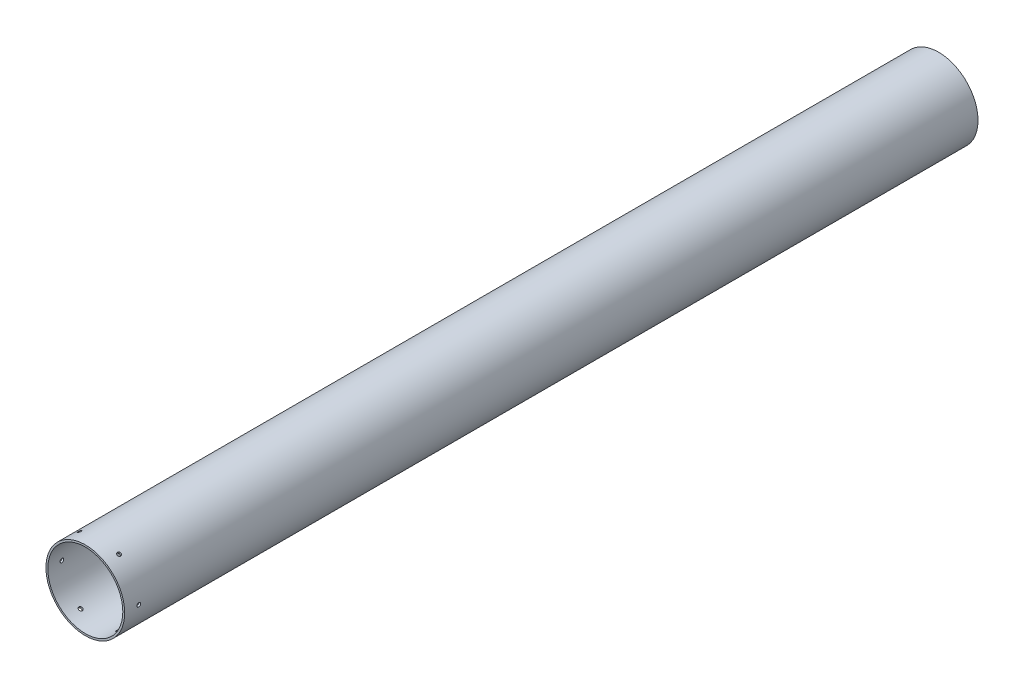
SolidWorks part; units mm, degrees
other "DetailItem1"
other "DetailItem2"
material "Default"
ref_plane "Front Plane" through (0, 0, 0) normal (0, 0, 1) x (1, 0, 0)
ref_plane "Top Plane" through (0, 0, 0) normal (0, 1, 0) x (1, 0, 0)
ref_plane "Right Plane" through (0, 0, 0) normal (1, 0, 0) x (0, 0, -1)
sketch "Sketch1" plane through (0, 0, 0) normal (1, 0, 0) x (0, 0, -1)
  line L0 (-455, 0) -> (455, 0) construction
  point P4 (0, 0)
  dimension "D1" = 910
ref_plane "Plane1" through (0, 0, 455) normal (0, 0, 1) x (1, 0, 0)
sketch "Sketch3" plane through (0, 0, 455) normal (0, 0, 1) x (1, 0, 0)
  circle A0 centre (0, 0) radius 42
  circle A1 centre (0, 0) radius 40
  dimension "D1" = 84
  dimension "D2" = 2
extrude "Boss-Extrude1" add sketch "Sketch3" against normal up to vertex (910 mm away) up to point (0, 0, -455)
ref_plane "Bolt Attachment" through (42, 0, 0) normal (1, 0, 0) x (0, 0, -1)
sketch "Sketch4" plane through (42, 0, 0) normal (1, 0, 0) x (0, 0, -1)
  line L0 (-455, 0) -> (-440, 0) construction
  line L1 (-455, 42) -> (-455, -42) construction
  circle A0 centre (-440, 0) radius 2
  dimension "D2" = 4
  dimension "D1" = 15
extrude "Cut-Extrude1" cut sketch "Sketch4" against normal up to surface (2 mm away)
pattern_circular "CirPattern1" count 6 over 360 about axis through (0, 0, 455) along (0, 0, 1) of "Cut-Extrude1"
